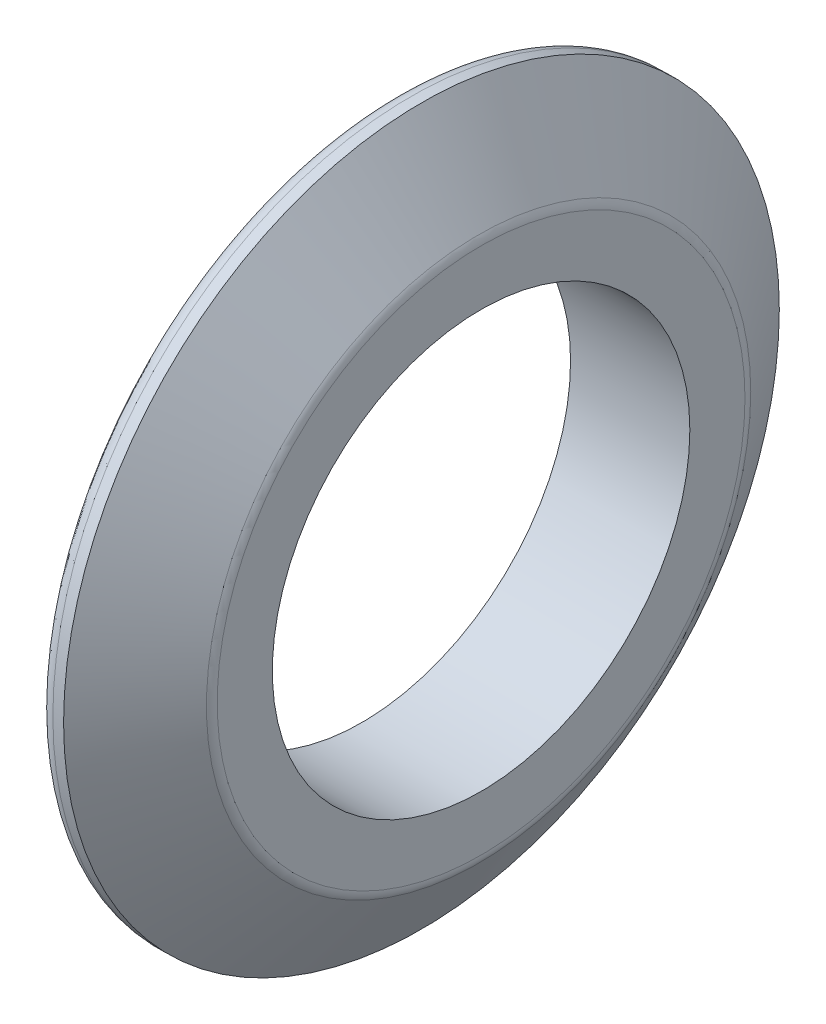
SolidWorks part; units mm, degrees
ref_plane "Front Plane" through (0, 0, 0) normal (0, 0, 1) x (1, 0, 0)
ref_plane "Top Plane" through (0, 0, 0) normal (0, 1, 0) x (1, 0, 0)
ref_plane "Right Plane" through (0, 0, 0) normal (1, 0, 0) x (0, 0, -1)
sketch "Sketch1" plane through (0, 0, 0) normal (0, 0, 1) x (1, 0, 0)
  line L0 (0, 0) -> (0, 7) construction
  line L1 (0, 0) -> (-4, 0) construction
  line L2 (0, 7) -> (0, 8.8486)
  line L3 (-0.084, 9.126) -> (-2, 12)
  line L4 (-2, 12) -> (-2.3596, 12)
  line L5 (-2.8447, 11.3787) -> (-2.1553, 8.6213)
  line L6 (-2.6404, 8) -> (-3.5, 8)
  line L7 (-4, 7.5) -> (-4, 7)
  line L8 (-4, 7) -> (0, 7)
  arc A0 (0, 8.8486) -> (-0.084, 9.126) centre (-0.5, 8.8486) ccw
  arc A1 (-3.5, 8) -> (-4, 7.5) centre (-3.5, 7.5) ccw
  arc A2 (-2.1553, 8.6213) -> (-2.6404, 8) centre (-2.6404, 8.5) cw
  arc A3 (-2.3596, 12) -> (-2.8447, 11.3787) centre (-2.3596, 11.5) ccw
  point P12 (0, 9)
  point P15 (-4, 8)
  point P18 (-2, 8)
  point P21 (-3, 12)
  dimension "D10" = 0.5
  dimension "D1" = 4
  dimension "D2" = 7
  dimension "D3" = 2
  dimension "D4" = 4
  dimension "D5" = 1
  dimension "D6" = 3
  dimension "D7" = 1
  dimension "D8" = 1
  dimension "D9" = 2
revolve "Revolve1" add sketch "Sketch1" angle 360 about L1
